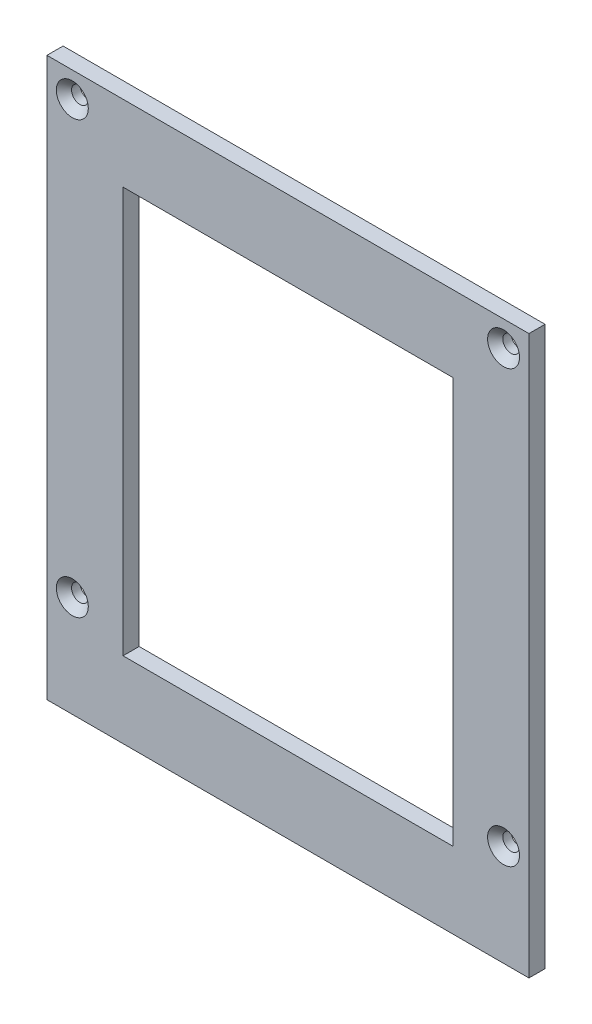
SolidWorks part; units mm, degrees
ref_plane "Front Plane" through (0, 0, 0) normal (0, 0, 1) x (1, 0, 0)
ref_plane "Top Plane" through (0, 0, 0) normal (0, 1, 0) x (1, 0, 0)
ref_plane "Right Plane" through (0, 0, 0) normal (1, 0, 0) x (0, 0, -1)
sketch "Sketch1" plane through (0, 0, 0) normal (0, 0, 1) x (1, 0, 0)
  line L1 (-95, 110) -> (95, 110)
  line L2 (-95, 110) -> (-95, -110)
  line L3 (-95, -110) -> (95, -110)
  line L4 (95, 110) -> (95, -110)
  line L5 (-65, 80) -> (65, 80)
  line L6 (-65, 80) -> (-65, -80)
  line L7 (-65, -80) -> (65, -80)
  line L8 (65, 80) -> (65, -80)
  point P4 (0, 110)
  point P6 (95, 0)
  point P7 (0, 80)
  point P12 (-65, 0)
  dimension "D1" = 220
  dimension "D2" = 190
  dimension "D3" = 30
  dimension "D4" = 30
extrude "Boss-Extrude1" add sketch "Sketch1" along normal blind 6.35
sketch "Sketch2" plane through (0, 0, 6.35) normal (0, 0, 1) x (1, 0, 0)
  line L0 (-95, 110) -> (-95, -110) construction
  line L1 (-95, -110) -> (95, -110) construction
  line L2 (95, -110) -> (95, 110) construction
  line L3 (95, 110) -> (-95, 110) construction
  point P0 (-85, 100)
  point P1 (85, 100)
  point P2 (85, -70)
  point P3 (-85, -70)
  dimension "D1" = 10
  dimension "D2" = 40
  dimension "D3" = 10
  dimension "D4" = 10
hole_wizard "CSK for M6 Countersunk Flat Head Screw1" positions "Sketch3" profile "Sketch4" countersink size "M6" standard "ISO"
sketch "Sketch3" plane through (0, 0, 6.35) normal (0, 0, 1) x (1, 0, 0)
  point P0 (-85, -70)
  point P3 (-85, 100)
  point P6 (85, 100)
  point P9 (85, -70)
sketch "Sketch4" plane through (-85, -70, 6.35) normal (1, 0, 0) x (0, -1, 0)
  line L0 (0, 0) -> (0, 46.9828)
  line L1 (0, 46.9828) -> (3.3, 45)
  line L2 (3.3, 45) -> (3.3, 2.9992)
  line L3 (3.3, 2.9992) -> (6.2992, 0)
  line L5 (6.2992, 0) -> (0, 0)
  line L6 (-3.3, 2.9992) -> (-6.2992, 0) construction
  line L10 (0, 46.9828) -> (-3.3, 45) construction
  line L11 (0, -6.35) -> (0, 107.95) construction
  dimension "Hole Dia." = 6.6
  dimension "Hole Depth" = 45
  dimension "Near C'Sink Dia." = 12.5984
  dimension "Near C'Sink Angle" = 90
  dimension "Drill Angle" = 118
equation "\"D3@Sketch2\"=\"D1@Sketch2\""
equation "\"D4@Sketch2\"=\"D1@Sketch2\""
